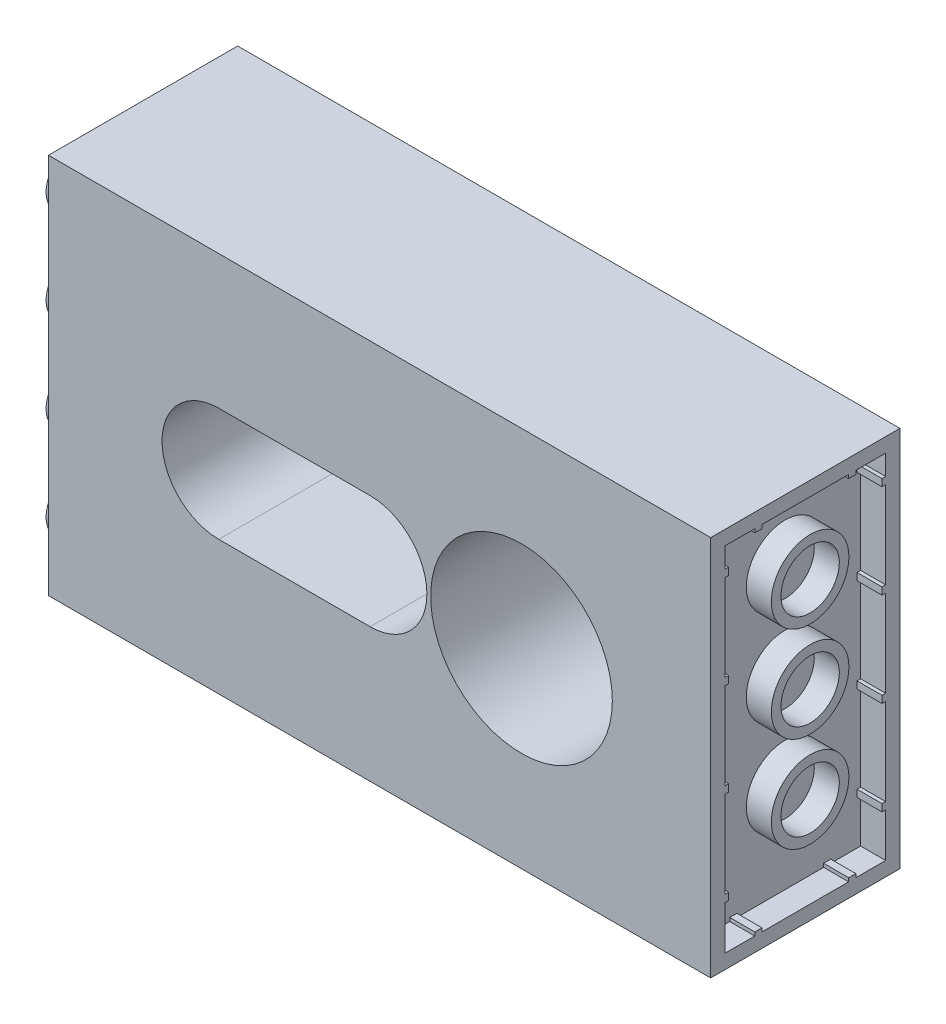
SolidWorks part; units mm, degrees
material "Custom Plastic"
ref_plane "Front Plane" through (0, 0, 0) normal (0, 0, 1) x (1, 0, 0)
ref_plane "Top Plane" through (0, 0, 0) normal (0, 1, 0) x (1, 0, 0)
ref_plane "Right Plane" through (0, 0, 0) normal (1, 0, 0) x (0, 0, -1)
sketch "Sketch1" plane through (0, 0, 0) normal (0, 1, 0) x (1, 0, 0)
  line L1 (-94.449, 51.0406) -> (-38.8865, 51.0406)
  line L2 (-94.449, 51.0406) -> (-94.449, 19.2906)
  line L3 (-94.449, 19.2906) -> (-38.8865, 19.2906)
  line L4 (-38.8865, 51.0406) -> (-38.8865, 19.2906)
  dimension "D1" = 55.5625
  dimension "D2" = 31.75
extrude "Boss-Extrude1" add sketch "Sketch1" along normal blind 28.575
sketch "Sketch2" plane through (0, 0, -19.2906) normal (0, 0, 1) x (1, 0, 0)
  line L1 (-94.449, 0) -> (-38.8865, 0) construction
  line L2 (-38.8865, 28.575) -> (-38.8865, 0) construction
  circle A0 centre (-54.7615, 16) radius 7.62
  dimension "D3" = 15.24
  dimension "D1" = 16
  dimension "D2" = 15.875
extrude "Cut-Extrude1" cut sketch "Sketch2" against normal blind 13.335
sketch "Sketch3" plane through (0, 0, -19.2906) normal (0, 0, 1) x (1, 0, 0)
  line L0 (-94.449, 28.575) -> (-38.8865, 28.575) construction
  line L1 (-94.449, 28.575) -> (-38.8865, 28.575)
  line L2 (-80.1615, 16) -> (-67.4615, 16) construction
  line L3 (-80.1615, 20.7625) -> (-67.4615, 20.7625)
  line L4 (-80.1615, 11.2375) -> (-67.4615, 11.2375)
  line L6 (-94.449, 0) -> (-38.8865, 0) construction
  arc A0 (-80.1615, 20.7625) -> (-80.1615, 11.2375) centre (-80.1615, 16) ccw
  circle A1 centre (-54.7615, 16) radius 7.62
  circle A2 centre (-54.7615, 16) radius 7.62
  arc A3 (-67.4615, 11.2375) -> (-67.4615, 20.7625) centre (-67.4615, 16) ccw
  point P7 (-73.8115, 16)
  dimension "D4" = 4.7625
  dimension "D5" = 16
  dimension "D2" = 12.7
  dimension "D3" = 12.7
  dimension "D1" = 0
extrude "Cut-Extrude2" cut sketch "Sketch3" against normal blind 12.7
sketch "Sketch4" plane through (0, 0, -31.9906) normal (0, 0, 1) x (1, 0, 0)
  line L2 (-80.1615, 11.2375) -> (-67.4615, 11.2375)
  line L3 (-67.4615, 20.7625) -> (-80.1615, 20.7625)
  line L4 (-80.1615, 11.2375) -> (-67.4615, 11.2375)
  line L5 (-67.4615, 20.7625) -> (-80.1615, 20.7625)
  arc A2 (-67.4615, 11.2375) -> (-67.4615, 20.7625) centre (-67.4615, 16) ccw
  arc A3 (-80.1615, 20.7625) -> (-80.1615, 11.2375) centre (-80.1615, 16) ccw
  arc A4 (-67.4615, 11.2375) -> (-67.4615, 20.7625) centre (-67.4615, 16) ccw
  arc A5 (-80.1615, 20.7625) -> (-80.1615, 11.2375) centre (-80.1615, 16) ccw
  circle A6 centre (-80.1615, 16) radius 1.8415
  circle A7 centre (-67.4615, 16) radius 1.8415
  dimension "D2" = 3.683
  dimension "D3" = 3.683
  dimension "D1" = 0
extrude "Cut-Extrude3" cut sketch "Sketch4" against normal blind 25.4 contours A7 | A6
sketch "Sketch5" plane through (0, 0, -51.0406) normal (0, 0, -1) x (-1, 0, 0)
  line L2 (67.4615, 11.2375) -> (80.1615, 11.2375)
  line L3 (80.1615, 20.7625) -> (67.4615, 20.7625)
  line L4 (38.8865, 0) -> (94.449, 0)
  line L5 (94.449, 0) -> (94.449, 28.575)
  line L6 (94.449, 28.575) -> (38.8865, 28.575)
  line L7 (38.8865, 28.575) -> (38.8865, 0)
  line L8 (38.8865, 0) -> (94.449, 0)
  line L9 (94.449, 0) -> (94.449, 28.575)
  line L10 (94.449, 28.575) -> (38.8865, 28.575)
  line L11 (38.8865, 28.575) -> (38.8865, 0)
  line L12 (67.4615, 11.2375) -> (80.1615, 11.2375)
  line L13 (80.1615, 20.7625) -> (67.4615, 20.7625)
  arc A2 (67.4615, 20.7625) -> (67.4615, 11.2375) centre (67.4615, 16) ccw
  arc A3 (80.1615, 11.2375) -> (80.1615, 20.7625) centre (80.1615, 16) ccw
  arc A4 (67.4615, 20.7625) -> (67.4615, 11.2375) centre (67.4615, 16) ccw
  arc A5 (80.1615, 11.2375) -> (80.1615, 20.7625) centre (80.1615, 16) ccw
  dimension "D1" = 0
  dimension "D2" = 0
extrude "Cut-Extrude4" cut sketch "Sketch5" against normal blind 17.78 contours L13 A4 L12 A5
sketch "Sketch6" plane through (0, 0, -51.0406) normal (0, 0, -1) x (-1, 0, 0)
  line L4 (38.8865, 0) -> (94.449, 0)
  line L5 (94.449, 0) -> (94.449, 28.575)
  line L6 (94.449, 28.575) -> (38.8865, 28.575)
  line L7 (38.8865, 28.575) -> (38.8865, 0)
  line L8 (38.8865, 0) -> (94.449, 0)
  line L9 (94.449, 0) -> (94.449, 28.575)
  line L10 (94.449, 28.575) -> (38.8865, 28.575)
  line L11 (38.8865, 28.575) -> (38.8865, 0)
  dimension "D1" = 0
extrude "Cut-Extrude5" cut sketch "Sketch6" against normal blind 15.875
sketch "Sketch7" plane through (0, 0, -32.6256) normal (0, 0, 1) x (1, 0, 0)
  line L0 (-94.449, 0) -> (-38.8865, 0) construction
  circle A0 centre (-54.7615, 16) radius 2.7781
  dimension "D2" = 5.5562
  dimension "D1" = 16
extrude "Cut-Extrude7" cut sketch "Sketch7" against normal blind 7.9375
sketch "Sketch10" plane through (0, 28.575, 0) normal (0, 1, 0) x (1, 0, 0)
  line L8 (-38.8865, 19.2906) -> (-38.8865, 20.9629)
  line L9 (-38.8865, 20.9629) -> (-38.8865, 25.3683)
  line L10 (-38.8865, 25.3683) -> (-38.8865, 28.9629)
  line L11 (-38.8865, 28.9629) -> (-38.8865, 33.3683)
  line L12 (-38.8865, 33.3683) -> (-38.8865, 35.1656)
  line L13 (-38.8865, 35.1656) -> (-94.449, 35.1656)
  line L14 (-94.449, 35.1656) -> (-94.449, 19.2906)
  line L15 (-94.449, 19.2906) -> (-38.8865, 19.2906)
  line L16 (-38.8865, 19.2906) -> (-38.8865, 20.9629)
  line L17 (-38.8865, 20.9629) -> (-38.8865, 25.3683)
  line L18 (-38.8865, 25.3683) -> (-38.8865, 28.9629)
  line L19 (-38.8865, 28.9629) -> (-38.8865, 33.3683)
  line L20 (-38.8865, 33.3683) -> (-38.8865, 35.1656)
  line L21 (-38.8865, 35.1656) -> (-94.449, 35.1656)
  line L22 (-94.449, 35.1656) -> (-94.449, 19.2906)
  line L23 (-94.449, 19.2906) -> (-38.8865, 19.2906)
  dimension "D1" = 0
extrude "Boss-Extrude3" add sketch "Sketch10" along normal blind 4
sketch "Sketch11" plane through (0, 0, -19.2906) normal (0, 0, 1) x (1, 0, 0)
  line L3 (-94.449, 32) -> (-38.8865, 32)
  line L4 (-94.449, 0) -> (-38.8865, 0)
  line L5 (-38.8865, 0) -> (-38.8865, 32.575)
  line L6 (-38.8865, 32.575) -> (-94.449, 32.575)
  line L7 (-94.449, 32.575) -> (-94.449, 0)
  line L9 (-38.8865, 32) -> (-38.8865, 32.575)
  line L10 (-38.8865, 32.575) -> (-94.449, 32.575)
  dimension "D1" = 0
extrude "Cut-Extrude8" cut sketch "Sketch11" against normal through all and the other way through all
sketch "Sketch19" plane through (-38.8865, 0, 0) normal (1, 0, 0) x (0, 0, -1)
  line L1 (20.4906, 30.8) -> (22.9906, 30.8)
  line L2 (20.4906, 30.8) -> (20.4906, 29.1028)
  line L3 (20.4906, 1.2) -> (22.9906, 1.2)
  line L4 (33.9656, 30.8) -> (33.9656, 29.1028)
  line L8 (20.4906, 20.6288) -> (20.7906, 20.6288)
  line L9 (20.4906, 29.1028) -> (20.7906, 29.1028)
  line L10 (19.2906, 32) -> (19.2906, 0) construction
  line L11 (20.4906, 28.5028) -> (20.7906, 28.5028)
  line L12 (20.7906, 29.1028) -> (20.7906, 28.5028)
  line L13 (33.9656, 29.1028) -> (33.6656, 29.1028)
  line L14 (31.4656, 30.8) -> (33.9656, 30.8)
  line L15 (33.9656, 28.5028) -> (33.6656, 28.5028)
  line L16 (33.6656, 29.1028) -> (33.6656, 28.5028)
  line L17 (20.7906, 21.2288) -> (20.7906, 20.6288)
  line L18 (20.4906, 21.2288) -> (20.7906, 21.2288)
  line L19 (33.9656, 20.6288) -> (33.6656, 20.6288)
  line L20 (33.6656, 21.2288) -> (33.6656, 20.6288)
  line L21 (33.9656, 21.2288) -> (33.6656, 21.2288)
  line L22 (20.4906, 12.7548) -> (20.7906, 12.7548)
  line L23 (20.7906, 13.3548) -> (20.7906, 12.7548)
  line L24 (20.4906, 13.3548) -> (20.7906, 13.3548)
  line L25 (33.9656, 12.7548) -> (33.6656, 12.7548)
  line L26 (33.6656, 13.3548) -> (33.6656, 12.7548)
  line L27 (33.9656, 13.3548) -> (33.6656, 13.3548)
  line L28 (20.4906, 4.8808) -> (20.7906, 4.8808)
  line L29 (20.7906, 5.4808) -> (20.7906, 4.8808)
  line L30 (20.4906, 5.4808) -> (20.7906, 5.4808)
  line L31 (33.9656, 4.8808) -> (33.6656, 4.8808)
  line L32 (33.6656, 5.4808) -> (33.6656, 4.8808)
  line L33 (33.9656, 5.4808) -> (33.6656, 5.4808)
  line L34 (20.4906, 20.6288) -> (20.4906, 13.3548)
  line L35 (35.1656, 32) -> (35.1656, 0) construction
  line L36 (22.9906, 30.8) -> (22.9906, 30.5)
  line L37 (22.9906, 30.5) -> (23.5906, 30.5)
  line L38 (23.5906, 30.8) -> (23.5906, 30.5)
  line L39 (23.5906, 30.8) -> (30.8656, 30.8)
  line L40 (30.8656, 30.8) -> (30.8656, 30.5)
  line L41 (30.8656, 30.5) -> (31.4656, 30.5)
  line L42 (31.4656, 30.8) -> (31.4656, 30.5)
  line L43 (31.4656, 1.2) -> (31.4656, 1.5)
  line L44 (30.8656, 1.5) -> (31.4656, 1.5)
  line L45 (30.8656, 1.2) -> (30.8656, 1.5)
  line L46 (23.5906, 1.2) -> (23.5906, 1.5)
  line L47 (22.9906, 1.5) -> (23.5906, 1.5)
  line L48 (22.9906, 1.2) -> (22.9906, 1.5)
  line L49 (20.4906, 12.7548) -> (20.4906, 5.4808)
  line L50 (33.9656, 20.6288) -> (33.9656, 13.3548)
  line L51 (33.9656, 12.7548) -> (33.9656, 5.4808)
  line L52 (33.9656, 4.8808) -> (33.9656, 1.2)
  line L53 (20.4906, 4.8808) -> (20.4906, 1.2)
  line L54 (23.5906, 1.2) -> (30.8656, 1.2)
  line L55 (31.4656, 1.2) -> (33.9656, 1.2)
  line L56 (33.9656, 28.5028) -> (33.9656, 21.2288)
  line L57 (20.4906, 28.5028) -> (20.4906, 21.2288)
  line L58 (19.2906, 0) -> (35.1656, 0) construction
  line L59 (19.2906, 32) -> (35.1656, 32) construction
  circle A0 centre (27.6312, 24.8028) radius 3.255
  circle A1 centre (27.6312, 24.8028) radius 2.45
  circle A2 centre (27.6312, 16.8028) radius 3.255
  circle A3 centre (27.6312, 16.8028) radius 2.45
  circle A4 centre (27.6312, 8.8028) radius 3.255
  circle A5 centre (27.6312, 8.8028) radius 2.45
  dimension "D6" = 6.51
  dimension "D7" = 4.9
  dimension "D2" = 1.2
  dimension "D3" = 1.2
  dimension "D4" = 1.2
  dimension "D5" = 1.2
  dimension "D10" = 0.6
  dimension "D11" = 0.6
  dimension "D12" = 0.3
  dimension "D13" = 0.3
  dimension "D14" = 4
  dimension "D15" = 0.6
  dimension "D16" = 0.6
  dimension "D17" = 0.3
  dimension "D18" = 0.3
  dimension "D8" = 3
extrude "Cut-Extrude11" cut sketch "Sketch19" against normal blind 2.1 contours A1 | A3 | A5 | L11 L57 L18 L17 L8 L34 L24 L23 L22 L49 L30 L29 L28 L53 L3 L48 L47 L46 L54 L45 L44 L43 L55 L52 L31 L32 L33 L51 L25 L26 L27 L50 L19 L20 L21 L56 L15 L16 L13 L4 L14 L42 L41 L40 L39 L38 L37 L36 L1 L2 L9
sketch "Sketch20" plane through (-94.449, 0, 0) normal (-1, 0, 0) x (0, 0, 1)
  line L0 (-19.2906, 32) -> (-19.2906, 0) construction
  line L1 (-35.1656, 0) -> (-19.2906, 0) construction
  circle A0 centre (-23.2906, 4) radius 2.4
  circle A1 centre (-31.2906, 4) radius 2.4
  circle A2 centre (-31.2906, 11.874) radius 2.4
  circle A3 centre (-23.2906, 11.874) radius 2.4
  circle A4 centre (-31.2906, 19.748) radius 2.4
  circle A5 centre (-23.2906, 19.748) radius 2.4
  circle A6 centre (-31.2906, 27.622) radius 2.4
  circle A7 centre (-23.2906, 27.622) radius 2.4
  dimension "D1" = 4.8
  dimension "D2" = 4
  dimension "D4" = 4.8
  dimension "D3" = 8
  dimension "D5" = 4
  dimension "D6" = 4
extrude "Boss-Extrude4" add sketch "Sketch20" along normal blind 1.8
